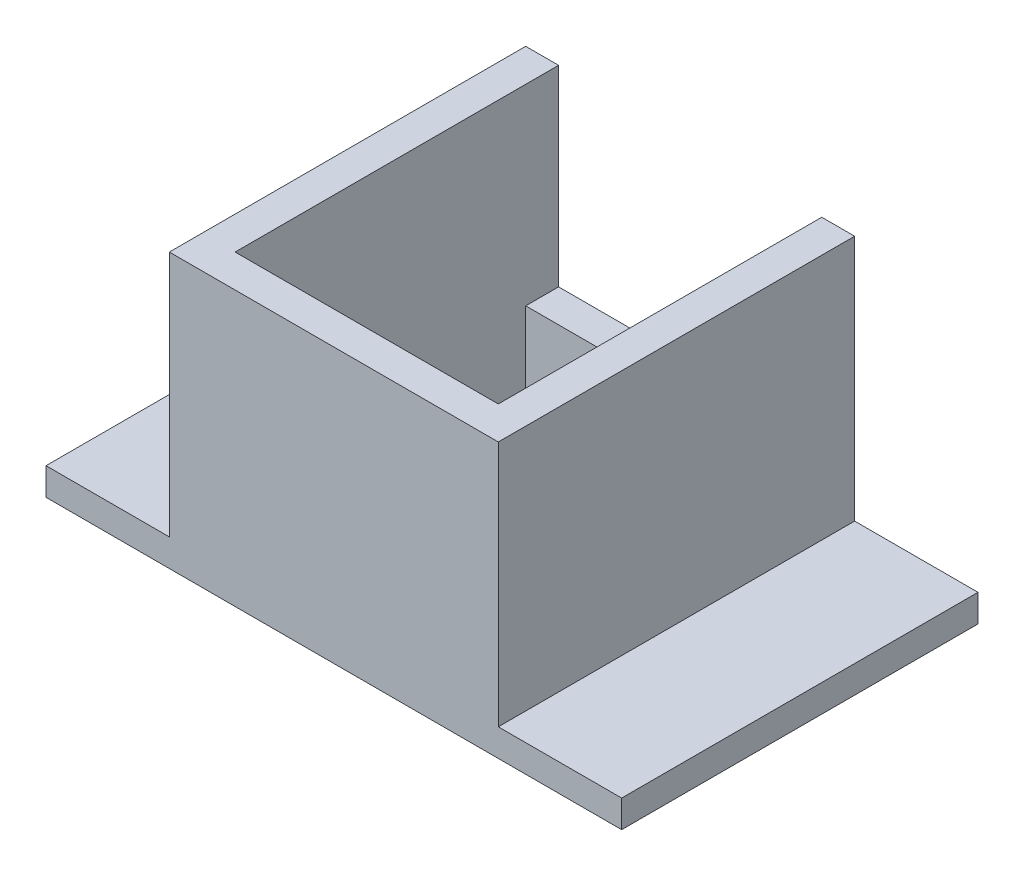
SolidWorks part; units mm, degrees
ref_plane "Front Plane" through (0, 0, 0) normal (0, 0, 1) x (1, 0, 0)
ref_plane "Top Plane" through (0, 0, 0) normal (0, 1, 0) x (1, 0, 0)
ref_plane "Right Plane" through (0, 0, 0) normal (1, 0, 0) x (0, 0, -1)
sketch "Sketch1" plane through (0, 0, 0) normal (0, 1, 0) x (1, 0, 0)
  line L0 (-4.8, 5.3) -> (-4.8, -5.3)
  line L1 (-6, 6.5) -> (6, 6.5)
  line L2 (-6, 6.5) -> (-6, -6.5)
  line L3 (-6, -6.5) -> (6, -6.5)
  line L4 (6, 6.5) -> (6, -6.5)
  line L5 (-6, 6.5) -> (6, -6.5) construction
  line L6 (-6, -6.5) -> (6, 6.5) construction
  line L7 (-4.8, -5.3) -> (4.8, -5.3)
  line L8 (4.8, 5.3) -> (4.8, -5.3)
  line L9 (-4.8, 5.3) -> (4.8, 5.3)
  point P0 (0, 0)
  dimension "D1" = 12
  dimension "D2" = 13
  dimension "D3" = 1.2
extrude "Boss-Extrude1" add sketch "Sketch1" along normal blind 10
sketch "Sketch2" plane through (0, 0, 0) normal (0, 1, 0) x (1, 0, 0)
  line L0 (-6, 6.5) -> (-10.5, 6.5)
  line L1 (-6, -6.5) -> (-10.5, -6.5)
  line L2 (-10.5, -6.5) -> (-10.5, 6.5)
  line L3 (-6, 6.5) -> (-6, -6.5)
  line L4 (0, 0) -> (0, 7.8091) construction
  line L5 (6, 6.5) -> (10.5, 6.5)
  line L6 (10.5, -6.5) -> (10.5, 6.5)
  line L7 (6, -6.5) -> (10.5, -6.5)
  line L8 (6, 6.5) -> (6, -6.5)
  dimension "D1" = 4.5
extrude "Boss-Extrude2" add sketch "Sketch2" along normal blind 1
sketch "Sketch3" plane through (0, 10, 0) normal (0, 1, 0) x (1, 0, 0)
  line L0 (-4.8, 5.3) -> (-4.8, 6.5)
  line L1 (6, 6.5) -> (-6, 6.5) construction
  line L2 (4.8, 5.3) -> (4.8, 6.5)
  line L3 (4.8, 6.5) -> (-4.8, 6.5)
  line L4 (-4.8, 5.3) -> (4.8, 5.3)
extrude "Cut-Extrude1" cut sketch "Sketch3" against normal blind 7
